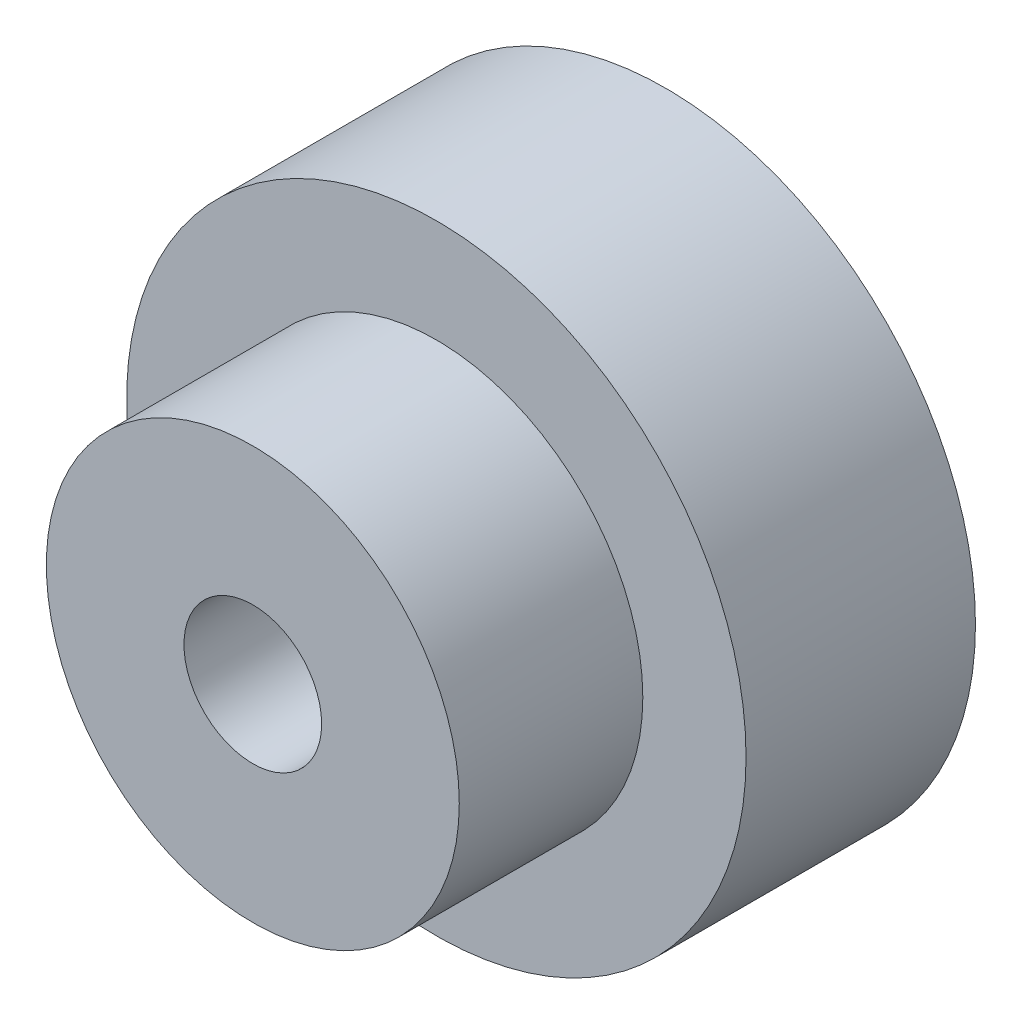
SolidWorks part; units mm, degrees
ref_plane "前视基准面" through (0, 0, 0) normal (0, 0, 1) x (1, 0, 0)
ref_plane "上视基准面" through (0, 0, 0) normal (0, 1, 0) x (1, 0, 0)
ref_plane "右视基准面" through (0, 0, 0) normal (1, 0, 0) x (0, 0, -1)
sketch "草图1" plane through (0, 0, 0) normal (0, 0, 1) x (1, 0, 0)
  circle A0 centre (0, 0) radius 13.5
  dimension "D1" = 27
extrude "凸台-拉伸1" add sketch "草图1" along normal blind 10
sketch "草图2" plane through (0, 0, 10) normal (0, 0, 1) x (1, 0, 0)
  circle A0 centre (0, 0) radius 9
  dimension "D1" = 18
extrude "凸台-拉伸2" add sketch "草图2" along normal blind 8
sketch "草图3" plane through (0, 0, 18) normal (0, 0, 1) x (1, 0, 0)
  circle A0 centre (0, 0) radius 3
  dimension "D1" = 6
extrude "切除-拉伸1" cut sketch "草图3" against normal through all
